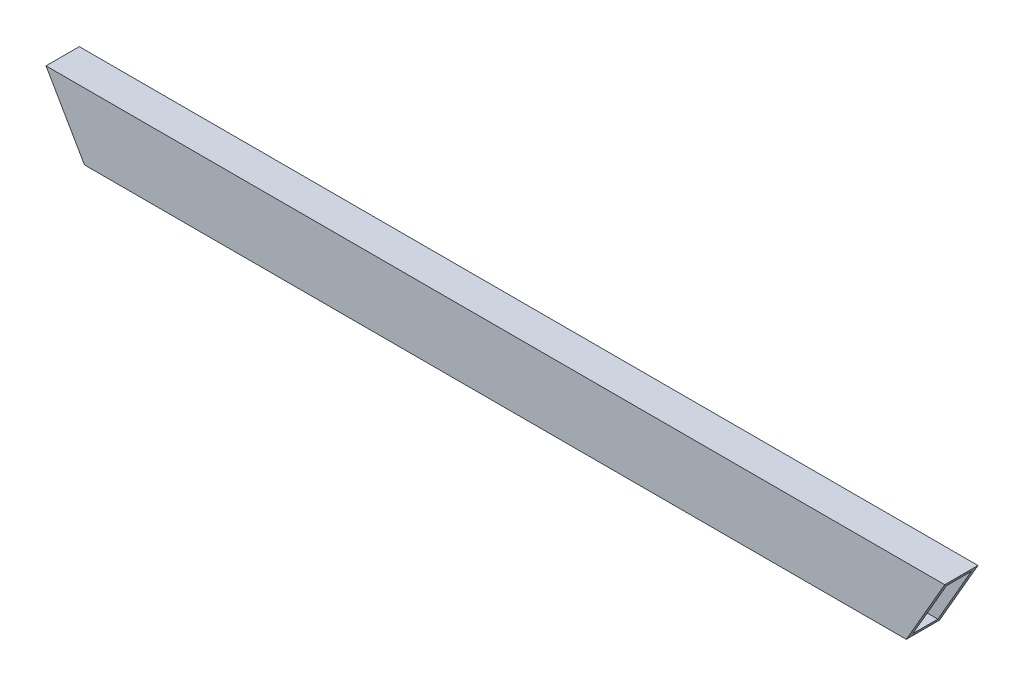
SolidWorks part; units mm, degrees
ref_plane "Front Plane" through (0, 0, 0) normal (0, 0, 1) x (1, 0, 0)
ref_plane "Top Plane" through (0, 0, 0) normal (0, 1, 0) x (1, 0, 0)
ref_plane "Right Plane" through (0, 0, 0) normal (1, 0, 0) x (0, 0, -1)
sketch "Sketch1" plane through (0, 0, 0) normal (1, 0, 0) x (0, 0, -1)
  line L1 (-9.525, -22.225) -> (9.525, -22.225)
  line L2 (-9.525, -22.225) -> (-9.525, 22.225)
  line L3 (-9.525, 22.225) -> (9.525, 22.225)
  line L4 (9.525, -22.225) -> (9.525, 22.225)
  line L5 (-9.525, -22.225) -> (9.525, 22.225) construction
  line L6 (-9.525, 22.225) -> (9.525, -22.225) construction
  line L7 (-12.7, -25.4) -> (12.7, -25.4)
  line L8 (-12.7, -25.4) -> (-12.7, 25.4)
  line L9 (-12.7, 25.4) -> (12.7, 25.4)
  line L10 (12.7, -25.4) -> (12.7, 25.4)
  line L11 (-12.7, -25.4) -> (12.7, 25.4) construction
  line L12 (-12.7, 25.4) -> (12.7, -25.4) construction
  point P0 (0, 0)
  point P6 (0, 0)
  dimension "D1" = 25.4
  dimension "D2" = 50.8
  dimension "D3" = 3.175
  dimension "D4" = 3.175
extrude "Boss-Extrude1" add sketch "Sketch1" along normal mid plane 685.8
sketch "Sketch2" plane through (0, 0, -12.7) normal (0, 0, -1) x (-1, 0, 0)
  line L0 (342.9, 25.4) -> (313.5706, -25.4)
  line L1 (-342.9, -25.4) -> (342.9, -25.4) construction
  line L3 (0, 13.97) -> (0, -13.97) construction
  line L4 (-342.9, 25.4) -> (-313.5706, -25.4)
  line M2 (342.9, -25.4) -> (342.9, 25.4)
  line M4 (-342.9, 25.4) -> (-342.9, -25.4)
  line M5 (-342.9, -25.4) -> (342.9, -25.4)
  dimension "D1" = 60
extrude "Cut-Extrude1" cut sketch "Sketch2" against normal through all and the other way through all contours L0 M2 M5 | L4 M4 M5
